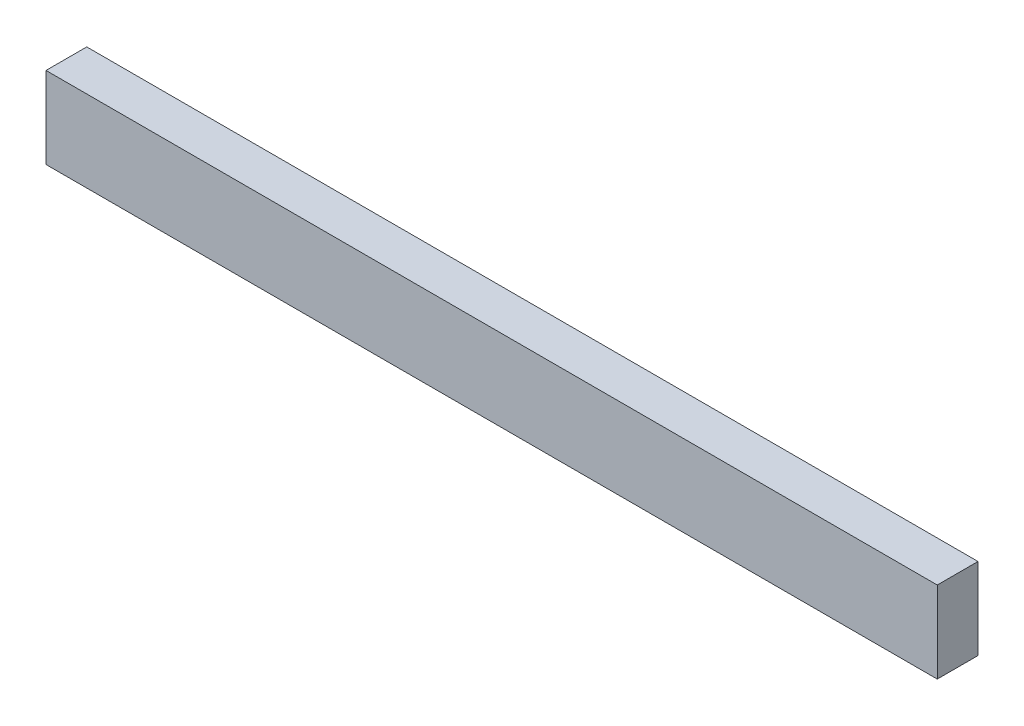
SolidWorks part; units mm, degrees
ref_plane "Front Plane" through (0, 0, 0) normal (0, 0, 1) x (1, 0, 0)
ref_plane "Top Plane" through (0, 0, 0) normal (0, 1, 0) x (1, 0, 0)
ref_plane "Right Plane" through (0, 0, 0) normal (1, 0, 0) x (0, 0, -1)
sketch "Sketch1" plane through (0, 0, 0) normal (0, 0, 1) x (1, 0, 0)
  line L1 (0, 0) -> (555.625, 0)
  line L2 (0, 0) -> (0, 50.8)
  line L3 (0, 50.8) -> (555.625, 50.8)
  line L4 (555.625, 0) -> (555.625, 50.8)
  dimension "D1" = 555.625
  dimension "D2" = 50.8
extrude "Boss-Extrude1" add sketch "Sketch1" along normal blind 25.4
